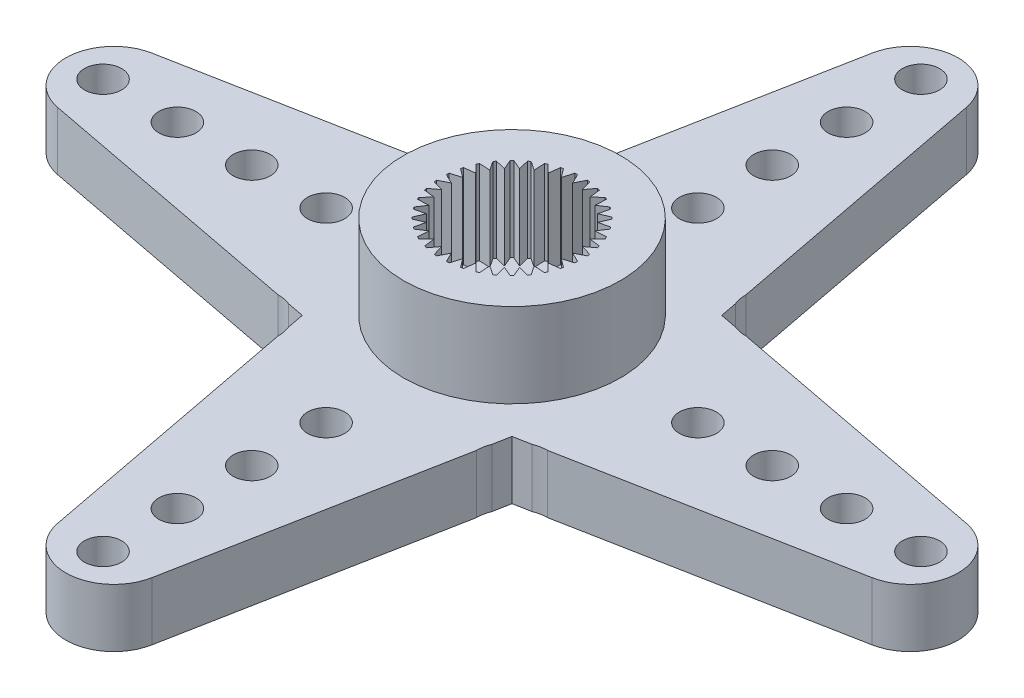
SolidWorks part; units mm, degrees
ref_plane "Front Plane" through (0, 0, 0) normal (0, 0, 1) x (1, 0, 0)
ref_plane "Top Plane" through (0, 0, 0) normal (0, 1, 0) x (1, 0, 0)
ref_plane "Right Plane" through (0, 0, 0) normal (1, 0, 0) x (0, 0, -1)
ref_plane "Plane1" through (0, 2.35, 0) normal (0, 1, 0) x (1, 0, 0)
sketch "Sketch1" plane through (0, 2.35, 0) normal (0, 1, 0) x (1, 0, 0)
  line L0 (-16.4286, -1.9) -> (-4.2305, -4.2305)
  line L1 (-4.2305, -4.2305) -> (-1.9, -16.4286)
  line L2 (1.9, -16.4286) -> (4.2305, -4.2305)
  line L3 (4.2305, -4.2305) -> (16.4286, -1.9)
  line L4 (16.4286, 1.9) -> (4.2305, 4.2305)
  line L5 (4.2305, 4.2305) -> (1.9, 16.4286)
  line L6 (-1.9, 16.4286) -> (-4.2305, 4.2305)
  line L7 (-4.2305, 4.2305) -> (-16.4286, 1.9)
  arc A0 (-1.9, -16.4286) -> (1.9, -16.4286) centre (0, -16.0656) ccw
  arc A1 (16.4286, -1.9) -> (16.4286, 1.9) centre (16.0656, 0) ccw
  arc A2 (1.9, 16.4286) -> (-1.9, 16.4286) centre (0, 16.0656) ccw
  arc A3 (-16.4286, 1.9) -> (-16.4286, -1.9) centre (-16.0656, 0) ccw
extrude "Boss-Extrude1" add sketch "Sketch1" against normal blind 2.35
sketch "Sketch2" plane through (0, 0, 0) normal (0, -1, 0) x (1, 0, 0)
  line L0 (4.1012, 4.9073) -> (4, 5.4371)
  arc A0 (4, 5.4371) -> (4.1012, 4.9073) centre (5.4371, 5.4371) ccw
extrude "Cut-Extrude1" cut sketch "Sketch2" against normal blind 2.35
sketch "Sketch3" plane through (0, 0, 0) normal (0, -1, 0) x (1, 0, 0)
  line L0 (5.4371, 4) -> (4.9073, 4.1012)
  arc A0 (4.9073, 4.1012) -> (5.4371, 4) centre (5.4371, 5.4371) ccw
extrude "Cut-Extrude2" cut sketch "Sketch3" against normal blind 2.35
sketch "Sketch4" plane through (0, 0, 0) normal (0, -1, 0) x (1, 0, 0)
  line L0 (4.9073, -4.1012) -> (5.4371, -4)
  arc A0 (5.4371, -4) -> (4.9073, -4.1012) centre (5.4371, -5.4371) ccw
extrude "Cut-Extrude3" cut sketch "Sketch4" against normal blind 2.35
sketch "Sketch5" plane through (0, 0, 0) normal (0, -1, 0) x (1, 0, 0)
  line L0 (4, -5.4371) -> (4.1012, -4.9073)
  arc A0 (4.1012, -4.9073) -> (4, -5.4371) centre (5.4371, -5.4371) ccw
extrude "Cut-Extrude4" cut sketch "Sketch5" against normal blind 2.35
sketch "Sketch6" plane through (0, 0, 0) normal (0, -1, 0) x (1, 0, 0)
  line L0 (-4.1012, -4.9073) -> (-4, -5.4371)
  arc A0 (-4, -5.4371) -> (-4.1012, -4.9073) centre (-5.4371, -5.4371) ccw
extrude "Cut-Extrude5" cut sketch "Sketch6" against normal blind 2.35
sketch "Sketch7" plane through (0, 0, 0) normal (0, -1, 0) x (1, 0, 0)
  line L0 (-5.4371, -4) -> (-4.9073, -4.1012)
  arc A0 (-4.9073, -4.1012) -> (-5.4371, -4) centre (-5.4371, -5.4371) ccw
extrude "Cut-Extrude6" cut sketch "Sketch7" against normal blind 2.35
sketch "Sketch8" plane through (0, 0, 0) normal (0, -1, 0) x (1, 0, 0)
  line L0 (-4.9073, 4.1012) -> (-5.4371, 4)
  arc A0 (-5.4371, 4) -> (-4.9073, 4.1012) centre (-5.4371, 5.4371) ccw
extrude "Cut-Extrude7" cut sketch "Sketch8" against normal blind 2.35
sketch "Sketch9" plane through (0, 0, 0) normal (0, -1, 0) x (1, 0, 0)
  line L0 (-4, 5.4371) -> (-4.1012, 4.9073)
  arc A0 (-4.1012, 4.9073) -> (-4, 5.4371) centre (-5.4371, 5.4371) ccw
extrude "Cut-Extrude8" cut sketch "Sketch9" against normal blind 2.35
sketch "Sketch10" plane through (0, 2.35, 0) normal (0, 1, 0) x (-1, 0, 0)
  circle A0 centre (0, 0) radius 4.375
extrude "Boss-Extrude2" add sketch "Sketch10" along normal blind 3.4
sketch "Sketch11" plane through (0, 5.75, 0) normal (0, 1, 0) x (-1, 0, 0)
  line L0 (0.6873, 2.7659) -> (0.4254, 2.4128)
  line L1 (0.4254, 2.4128) -> (0.3001, 2.8342)
  line L2 (0.1966, 2.8432) -> (0, 2.45)
  line L3 (0, 2.45) -> (-0.1966, 2.8432)
  line L4 (-0.3001, 2.8342) -> (-0.4254, 2.4128)
  line L5 (-0.4254, 2.4128) -> (-0.6873, 2.7659)
  line L6 (-0.7877, 2.739) -> (-0.8379, 2.3022)
  line L7 (-0.8379, 2.3022) -> (-1.1572, 2.6045)
  line L8 (-1.2513, 2.5606) -> (-1.225, 2.1218)
  line L9 (-1.225, 2.1218) -> (-1.5919, 2.364)
  line L10 (-1.677, 2.3044) -> (-1.5748, 1.8768)
  line L11 (-1.5748, 1.8768) -> (-1.9782, 2.0517)
  line L12 (-2.0517, 1.9782) -> (-1.8768, 1.5748)
  line L13 (-1.8768, 1.5748) -> (-2.3044, 1.677)
  line L14 (-2.364, 1.5919) -> (-2.1218, 1.225)
  line L15 (-2.1218, 1.225) -> (-2.5606, 1.2513)
  line L16 (-2.6045, 1.1572) -> (-2.3022, 0.8379)
  line L17 (-2.3022, 0.8379) -> (-2.739, 0.7877)
  line L18 (-2.7659, 0.6873) -> (-2.4128, 0.4254)
  line L19 (-2.4128, 0.4254) -> (-2.8342, 0.3001)
  line L20 (-2.8432, 0.1966) -> (-2.45, 0)
  line L21 (-2.45, 0) -> (-2.8432, -0.1966)
  line L22 (-2.8342, -0.3001) -> (-2.4128, -0.4254)
  line L23 (-2.4128, -0.4254) -> (-2.7659, -0.6873)
  line L24 (-2.739, -0.7877) -> (-2.3022, -0.8379)
  line L25 (-2.3022, -0.8379) -> (-2.6045, -1.1572)
  line L26 (-2.5606, -1.2513) -> (-2.1218, -1.225)
  line L27 (-2.1218, -1.225) -> (-2.364, -1.5919)
  line L28 (-2.3044, -1.677) -> (-1.8768, -1.5748)
  line L29 (-1.8768, -1.5748) -> (-2.0517, -1.9782)
  line L30 (-1.9782, -2.0517) -> (-1.5748, -1.8768)
  line L31 (-1.5748, -1.8768) -> (-1.677, -2.3044)
  line L32 (-1.5919, -2.364) -> (-1.225, -2.1218)
  line L33 (-1.225, -2.1218) -> (-1.2513, -2.5606)
  line L34 (-1.1572, -2.6045) -> (-0.8379, -2.3022)
  line L35 (-0.8379, -2.3022) -> (-0.7877, -2.739)
  line L36 (-0.6873, -2.7659) -> (-0.4254, -2.4128)
  line L37 (-0.4254, -2.4128) -> (-0.3001, -2.8342)
  line L38 (-0.1966, -2.8432) -> (0, -2.45)
  line L39 (0, -2.45) -> (0.1966, -2.8432)
  line L40 (0.3001, -2.8342) -> (0.4254, -2.4128)
  line L41 (0.4254, -2.4128) -> (0.6873, -2.7659)
  line L42 (0.7877, -2.739) -> (0.8379, -2.3022)
  line L43 (0.8379, -2.3022) -> (1.1572, -2.6045)
  line L44 (1.2513, -2.5606) -> (1.225, -2.1218)
  line L45 (1.225, -2.1218) -> (1.5919, -2.364)
  line L46 (1.677, -2.3044) -> (1.5748, -1.8768)
  line L47 (1.5748, -1.8768) -> (1.9782, -2.0517)
  line L48 (2.0517, -1.9782) -> (1.8768, -1.5748)
  line L49 (1.8768, -1.5748) -> (2.3044, -1.677)
  line L50 (2.364, -1.5919) -> (2.1218, -1.225)
  line L51 (2.1218, -1.225) -> (2.5606, -1.2513)
  line L52 (2.6045, -1.1572) -> (2.3022, -0.8379)
  line L53 (2.3022, -0.8379) -> (2.739, -0.7877)
  line L54 (2.7659, -0.6873) -> (2.4128, -0.4254)
  line L55 (2.4128, -0.4254) -> (2.8342, -0.3001)
  line L56 (2.8432, -0.1966) -> (2.45, 0)
  line L57 (2.45, 0) -> (2.8432, 0.1966)
  line L58 (2.8342, 0.3001) -> (2.4128, 0.4254)
  line L59 (2.4128, 0.4254) -> (2.7659, 0.6873)
  line L60 (2.739, 0.7877) -> (2.3022, 0.8379)
  line L61 (2.3022, 0.8379) -> (2.6045, 1.1572)
  line L62 (2.5606, 1.2513) -> (2.1218, 1.225)
  line L63 (2.1218, 1.225) -> (2.364, 1.5919)
  line L64 (2.3044, 1.677) -> (1.8768, 1.5748)
  line L65 (1.8768, 1.5748) -> (2.0517, 1.9782)
  line L66 (1.9782, 2.0517) -> (1.5748, 1.8768)
  line L67 (1.5748, 1.8768) -> (1.677, 2.3044)
  line L68 (1.5919, 2.364) -> (1.225, 2.1218)
  line L69 (1.225, 2.1218) -> (1.2513, 2.5606)
  line L70 (1.1572, 2.6045) -> (0.8379, 2.3022)
  line L71 (0.8379, 2.3022) -> (0.7877, 2.739)
  arc A0 (0.3001, 2.8342) -> (0.1966, 2.8432) centre (0, 0) ccw
  arc A1 (-0.1966, 2.8432) -> (-0.3001, 2.8342) centre (0, 0) ccw
  arc A2 (-0.6873, 2.7659) -> (-0.7877, 2.739) centre (0, 0) ccw
  arc A3 (-1.1572, 2.6045) -> (-1.2513, 2.5606) centre (0, 0) ccw
  arc A4 (-1.5919, 2.364) -> (-1.677, 2.3044) centre (0, 0) ccw
  arc A5 (-1.9782, 2.0517) -> (-2.0517, 1.9782) centre (0, 0) ccw
  arc A6 (-2.3044, 1.677) -> (-2.364, 1.5919) centre (0, 0) ccw
  arc A7 (-2.5606, 1.2513) -> (-2.6045, 1.1572) centre (0, 0) ccw
  arc A8 (-2.739, 0.7877) -> (-2.7659, 0.6873) centre (0, 0) ccw
  arc A9 (-2.8342, 0.3001) -> (-2.8432, 0.1966) centre (0, 0) ccw
  arc A10 (-2.8432, -0.1966) -> (-2.8342, -0.3001) centre (0, 0) ccw
  arc A11 (-2.7659, -0.6873) -> (-2.739, -0.7877) centre (0, 0) ccw
  arc A12 (-2.6045, -1.1572) -> (-2.5606, -1.2513) centre (0, 0) ccw
  arc A13 (-2.364, -1.5919) -> (-2.3044, -1.677) centre (0, 0) ccw
  arc A14 (-2.0517, -1.9782) -> (-1.9782, -2.0517) centre (0, 0) ccw
  arc A15 (-1.677, -2.3044) -> (-1.5919, -2.364) centre (0, 0) ccw
  arc A16 (-1.2513, -2.5606) -> (-1.1572, -2.6045) centre (0, 0) ccw
  arc A17 (-0.7877, -2.739) -> (-0.6873, -2.7659) centre (0, 0) ccw
  arc A18 (-0.3001, -2.8342) -> (-0.1966, -2.8432) centre (0, 0) ccw
  arc A19 (0.1966, -2.8432) -> (0.3001, -2.8342) centre (0, 0) ccw
  arc A20 (0.6873, -2.7659) -> (0.7877, -2.739) centre (0, 0) ccw
  arc A21 (1.1572, -2.6045) -> (1.2513, -2.5606) centre (0, 0) ccw
  arc A22 (1.5919, -2.364) -> (1.677, -2.3044) centre (0, 0) ccw
  arc A23 (1.9782, -2.0517) -> (2.0517, -1.9782) centre (0, 0) ccw
  arc A24 (2.3044, -1.677) -> (2.364, -1.5919) centre (0, 0) ccw
  arc A25 (2.5606, -1.2513) -> (2.6045, -1.1572) centre (0, 0) ccw
  arc A26 (2.739, -0.7877) -> (2.7659, -0.6873) centre (0, 0) ccw
  arc A27 (2.8342, -0.3001) -> (2.8432, -0.1966) centre (0, 0) ccw
  arc A28 (2.8432, 0.1966) -> (2.8342, 0.3001) centre (0, 0) ccw
  arc A29 (2.7659, 0.6873) -> (2.739, 0.7877) centre (0, 0) ccw
  arc A30 (2.6045, 1.1572) -> (2.5606, 1.2513) centre (0, 0) ccw
  arc A31 (2.364, 1.5919) -> (2.3044, 1.677) centre (0, 0) ccw
  arc A32 (2.0517, 1.9782) -> (1.9782, 2.0517) centre (0, 0) ccw
  arc A33 (1.677, 2.3044) -> (1.5919, 2.364) centre (0, 0) ccw
  arc A34 (1.2513, 2.5606) -> (1.1572, 2.6045) centre (0, 0) ccw
  arc A35 (0.7877, 2.739) -> (0.6873, 2.7659) centre (0, 0) ccw
extrude "Cut-Extrude9" cut sketch "Sketch11" against normal blind 3.4
hole_wizard "Ø8.8 (8.8) Diameter Hole1" positions "Sketch13" profile "Sketch12" hole size "Ø8.8" standard "ANSI Metric"
sketch "Sketch13" plane through (0, 0, 0) normal (0, -1, 0) x (-1, 0, 0)
  point P0 (0, 0)
sketch "Sketch12" plane through (0, 0, 0) normal (1, 0, 0) x (0, 0, -1)
  line L0 (0, 0) -> (0, 0.3)
  line L1 (0, 0.3) -> (4.4, 0.3)
  line L2 (4.4, 0.3) -> (4.4, 0)
  line L5 (4.4, 0) -> (0, 0)
  line L10 (0, 0.3) -> (-4.4, 0.3) construction
  line L11 (0, -6.35) -> (0, 107.95) construction
  dimension "Hole Dia." = 8.8
  dimension "Hole Depth" = 0.3
  dimension "Drill Angle" = 180
sketch "Sketch14" plane through (0, 0, 0) normal (0, 0, 1) x (1, 0, 0)
  line L0 (3.25, 0.3) -> (0, 0.3)
  line L1 (0, 0.3) -> (0, 0)
  line L2 (0, 0) -> (3.25, 0)
  line L3 (3.25, 0) -> (3.25, 0.3)
  line L4 (0, 0.3) -> (0, 0) construction
revolve "Revolve1" add sketch "Sketch14" angle 360 about L4
hole_wizard "Ø1.5 (1.5) Diameter Hole1" positions "Sketch16" profile "Sketch15" hole size "Ø1.5" standard "ANSI Metric"
sketch "Sketch16" plane through (0, 2.35, 0) normal (0, 1, 0) x (1, 0, 0)
  point P0 (0, -7.5)
  point P1 (0, -10.5)
  point P2 (0, -13.5)
  point P3 (0, -16.5)
  point P4 (7.5, 0)
  point P5 (10.5, 0)
  point P6 (13.5, 0)
  point P7 (16.5, 0)
  point P8 (0, 7.5)
  point P9 (0, 10.5)
  point P10 (0, 13.5)
  point P11 (0, 16.5)
  point P12 (-7.5, 0)
  point P13 (-10.5, 0)
  point P14 (-13.5, 0)
  point P15 (-16.5, 0)
sketch "Sketch15" plane through (0, 2.35, 7.5) normal (1, 0, 0) x (0, 0, 1)
  line L0 (0, 0) -> (0, 2.35)
  line L1 (0, 2.35) -> (0.75, 2.35)
  line L2 (0.75, 2.35) -> (0.75, 0)
  line L5 (0.75, 0) -> (0, 0)
  line L11 (0, -6.35) -> (0, 107.95) construction
  dimension "Thru Hole Dia." = 1.5
  dimension "Thru Hole Depth" = 2.35
hole_wizard "CBORE for M2.5 Hex Head Machine Screw1" positions "Sketch18" profile "Sketch17" counterbore size "M2.5" standard "ANSI Metric"
sketch "Sketch18" plane through (0, 0, 0) normal (0, -1, 0) x (-1, 0, 0)
  point P0 (0, 0)
sketch "Sketch17" plane through (0, 0, 0) normal (1, 0, 0) x (0, 0, -1)
  line L0 (0, 0) -> (0, 5.75)
  line L1 (0, 5.75) -> (1.5, 5.75)
  line L3 (1.5, 5.75) -> (1.5, 0.3)
  line L4 (1.5, 0.3) -> (2.75, 0.3)
  line L5 (2.75, 0.3) -> (2.75, 0)
  line L7 (2.75, 0) -> (0, 0)
  line L11 (0, -6.35) -> (0, 107.95) construction
  dimension "Thru Hole Dia." = 3
  dimension "Thru Hole Depth" = 5.75
  dimension "C'Bore Dia." = 5.5
  dimension "C'Bore Depth" = 0.3
